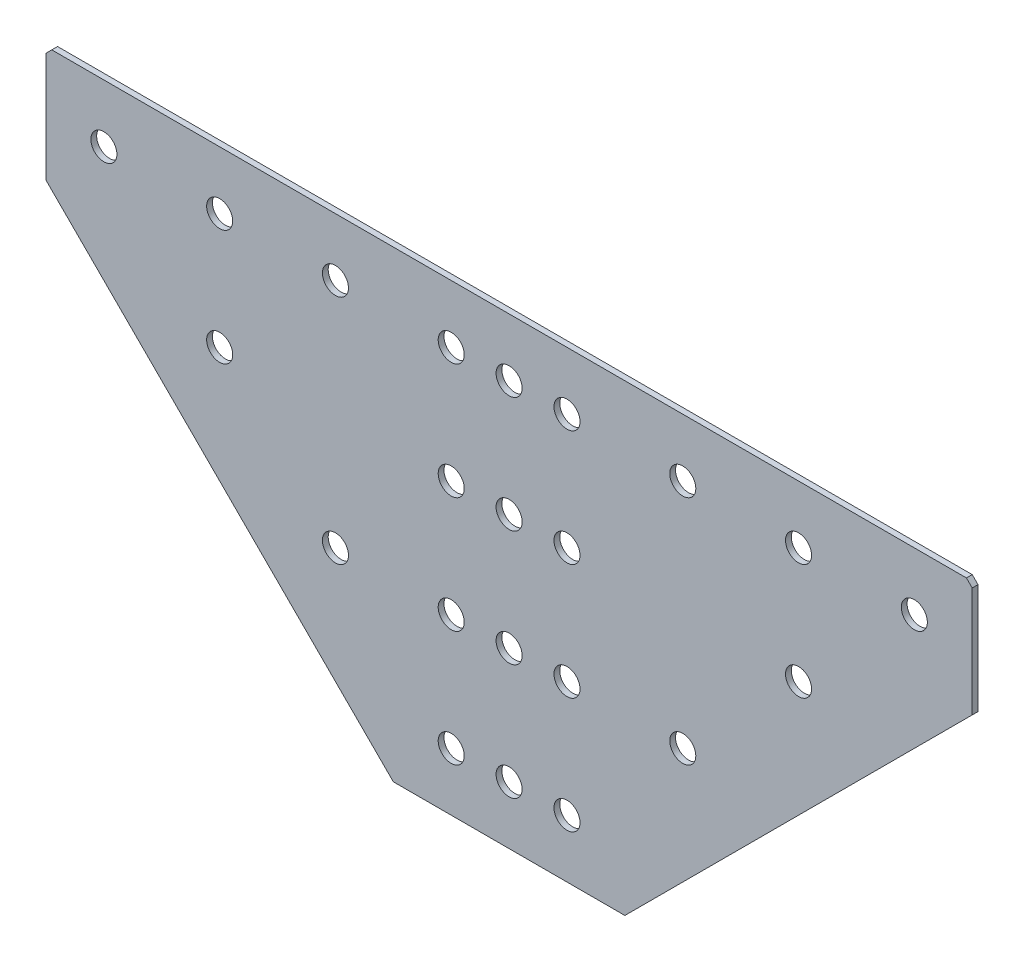
SolidWorks part; units mm, degrees
ref_plane "Спереди" through (0, 0, 0) normal (0, 0, 1) x (1, 0, 0)
ref_plane "Сверху" through (0, 0, 0) normal (0, 1, 0) x (1, 0, 0)
ref_plane "Справа" through (0, 0, 0) normal (1, 0, 0) x (0, 0, -1)
sketch "Эскиз1" plane through (0, 0, 0) normal (0, 0, 1) x (1, 0, 0)
  line L2 (160, -40) -> (40, -160)
  line L3 (40, -160) -> (-40, -160)
  line L4 (-40, -160) -> (-160, -40)
  line L6 (-160, -40) -> (-160, 0)
  line L7 (-160, 0) -> (160, 0)
  line L8 (160, 0) -> (160, -40)
  dimension "D1" = 320
  dimension "D2" = 160
  dimension "D3" = 80
  dimension "D4" = 40
extrude "Бобышка-Вытянуть1" add sketch "Эскиз1" along normal blind 2
chamfer "Фаска1" distance 2 angle 45 2 edges at (-160, 0, 1) (160, 0, 1)
hole_wizard "Отверстие с зазором M81" positions "Эскиз2" profile "Эскиз3" hole size "M8" standard "DIN" end condition through all
sketch "Эскиз2" plane through (0, 0, 2) normal (0, 0, 1) x (1, 0, 0)
  line L0 (0, 0) -> (0, -20) construction
  line L1 (0, -20) -> (20, -20) construction
  line L3 (0, -20) -> (-20, -20) construction
  line L5 (-20, -20) -> (-20, -60) construction
  line L6 (-20, -60) -> (-20, -100) construction
  line L7 (-20, -100) -> (-20, -140) construction
  line L9 (0, -20) -> (0, -60) construction
  line L10 (0, -60) -> (0, -100) construction
  line L11 (0, -100) -> (0, -140) construction
  line L13 (20, -20) -> (20, -60) construction
  line L14 (20, -60) -> (20, -100) construction
  line L15 (20, -100) -> (20, -140) construction
  line L17 (-20, -20) -> (-60, -20) construction
  line L18 (-60, -20) -> (-100, -20) construction
  line L19 (-100, -20) -> (-140, -20) construction
  line L21 (20, -20) -> (60, -20) construction
  line L22 (60, -20) -> (100, -20) construction
  line L23 (100, -20) -> (140, -20) construction
  line L25 (-100, -20) -> (-100, -60) construction
  line L27 (100, -20) -> (100, -60) construction
  line L29 (-60, -20) -> (-60, -100) construction
  line L31 (60, -20) -> (60, -100) construction
  point P2 (0, -20)
  point P4 (20, -20)
  point P8 (-20, -20)
  point P12 (-20, -60)
  point P13 (-20, -100)
  point P15 (-20, -140)
  point P20 (0, -60)
  point P21 (0, -100)
  point P23 (0, -140)
  point P28 (20, -60)
  point P30 (20, -100)
  point P32 (20, -140)
  point P37 (-60, -20)
  point P38 (-100, -20)
  point P39 (-140, -20)
  point P44 (60, -20)
  point P45 (100, -20)
  point P46 (140, -20)
  point P51 (-100, -60)
  point P55 (100, -60)
  point P59 (-60, -100)
  point P64 (60, -100)
  dimension "D1" = 20
  dimension "D2" = 40
  dimension "D3" = 80
sketch "Эскиз3" plane through (60, -100, 2) normal (1, 0, 0) x (0, -1, 0)
  line L0 (0, 0) -> (0, 2)
  line L1 (0, 2) -> (4.5, 2)
  line L2 (4.5, 2) -> (4.5, 0)
  line L5 (4.5, 0) -> (0, 0)
  line L11 (0, -6.35) -> (0, 107.95) construction
  dimension "Диаметр сквозного отверстия" = 9
  dimension "Глубина сквозного отверстия" = 2
